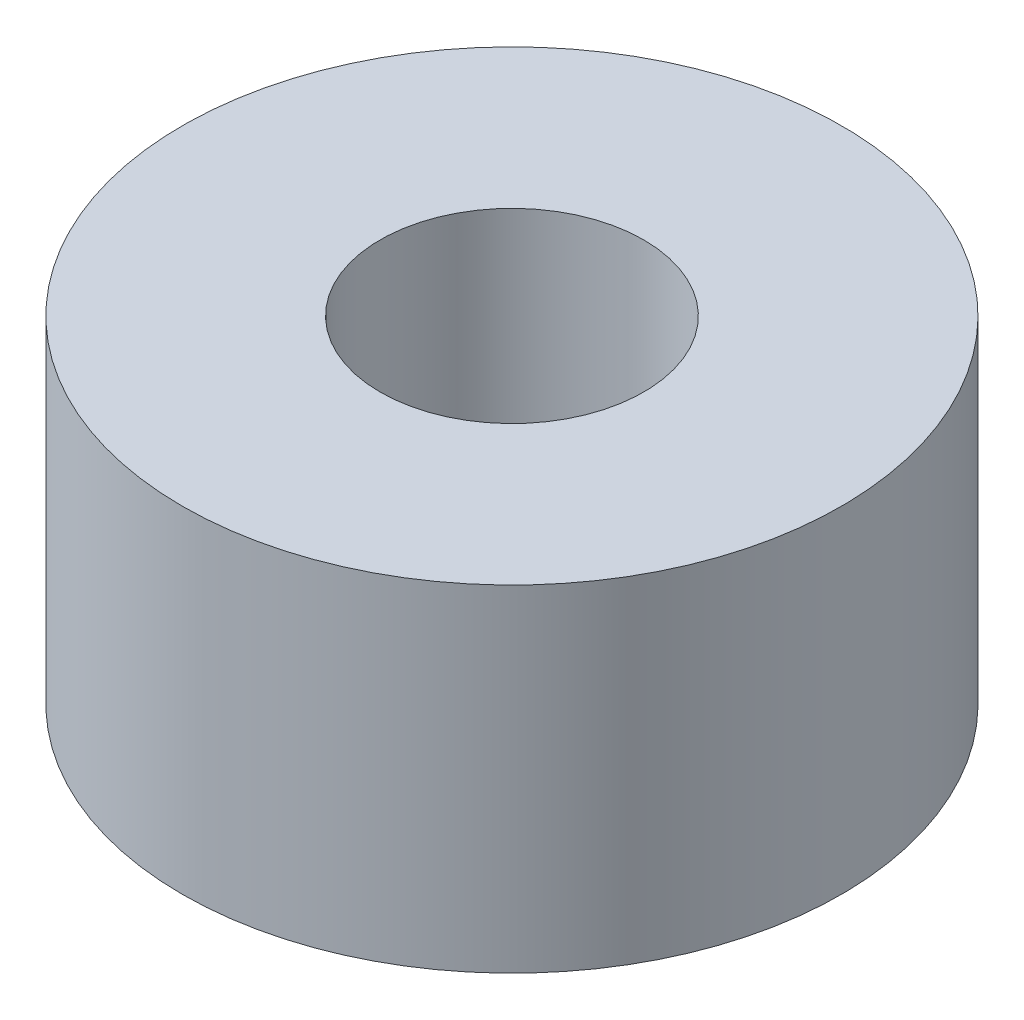
SolidWorks part; units mm, degrees
ref_plane "Front" through (0, 0, 0) normal (0, 0, 1) x (1, 0, 0)
ref_plane "Top" through (0, 0, 0) normal (0, 1, 0) x (1, 0, 0)
ref_plane "Right" through (0, 0, 0) normal (1, 0, 0) x (0, 0, -1)
sketch "Sketch2" plane through (0, 0, 0) normal (0, 1, 0) x (1, 0, 0)
  circle A0 centre (0, 0) radius 2
  circle A1 centre (0, 0) radius 5
  dimension "D1" = 4
  dimension "D2" = 3
extrude "Boss-Extrude1" add sketch "Sketch2" along normal mid plane 5.1
